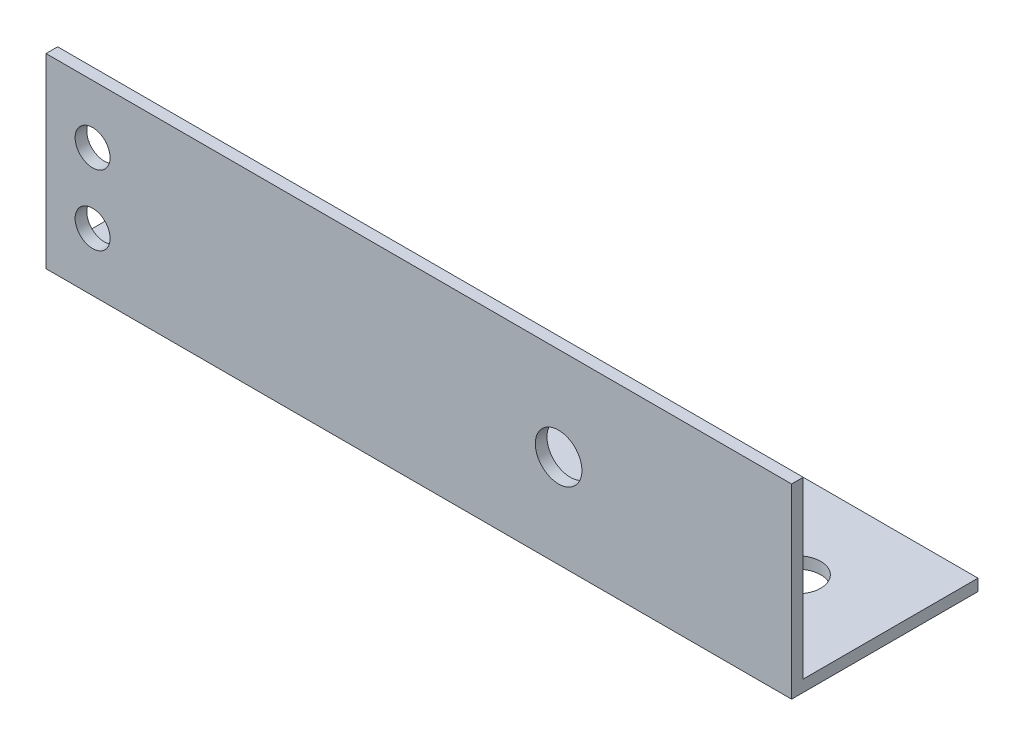
SolidWorks part; units mm, degrees
ref_plane "Front Plane" through (0, 0, 0) normal (0, 0, 1) x (1, 0, 0)
ref_plane "Top Plane" through (0, 0, 0) normal (0, 1, 0) x (1, 0, 0)
ref_plane "Right Plane" through (0, 0, 0) normal (1, 0, 0) x (0, 0, -1)
sketch "Sketch1" plane through (0, 0, 0) normal (1, 0, 0) x (0, 0, -1)
  line L0 (0, 0) -> (0, 25.4)
  line L1 (0, 25.4) -> (-1.5875, 25.4)
  line L2 (-1.5875, 25.4) -> (-1.5875, 1.5875)
  line L3 (-1.5875, 1.5875) -> (-25.4, 1.5875)
  line L4 (-25.4, 1.5875) -> (-25.4, 0)
  line L5 (-25.4, 0) -> (0, 0)
  dimension "D1" = 25.4
  dimension "D2" = 25.4
  dimension "D3" = 1.5875
  dimension "D4" = 1.5875
extrude "Boss-Extrude1" add sketch "Sketch1" along normal blind 101.6 contours L0 L1 L2 L3 L4 L5
sketch "Sketch2" plane through (0, 1.5875, 0) normal (0, 1, 0) x (1, 0, 0)
  line L0 (0, -13.4937) -> (101.6, -13.4937) construction
  line L1 (0, -1.5875) -> (0, -25.4) construction
  line L2 (101.6, -1.5875) -> (101.6, -25.4) construction
  circle A0 centre (12.7, -13.4937) radius 3.175
  circle A1 centre (88.9, -13.4937) radius 3.175
  dimension "D1" = 6.35
  dimension "D2" = 12.7
  dimension "D3" = 12.7
extrude "Cut-Extrude1" cut sketch "Sketch2" against normal blind 101.6
sketch "Sketch3" plane through (0, 0, 1.5875) normal (0, 0, 1) x (1, 0, 0)
  line L0 (0, 0) -> (0, 25.4) construction
  line L1 (0, 12.7) -> (101.6, 12.7) construction
  line L2 (101.6, 25.4) -> (101.6, 1.5875) construction
  line L3 (6.35, 7.9375) -> (6.35, 17.4625) construction
  circle A0 centre (69.85, 12.7) radius 3.175
  circle A1 centre (6.35, 17.4625) radius 2.3813
  circle A2 centre (6.35, 7.9375) radius 2.3813
  point P13 (6.35, 12.7)
  dimension "D2" = 4.7625
  dimension "D3" = 6.35
  dimension "D1" = 9.525
  dimension "D4" = 6.35
  dimension "D5" = 31.75
extrude "Cut-Extrude2" cut sketch "Sketch3" against normal blind 101.6
mirror "Mirror1" about plane through (101.6, 0, 0) normal (0, 0, 1) of "Boss-Extrude1", "Cut-Extrude1", "Cut-Extrude2"
sketch "Sketch4" plane through (0, 0, 0) normal (-1, 0, 0) x (0, 0, 1)
  line L0 (0, 0) -> (0, 25.4) construction
  line L1 (25.4, 0) -> (-25.4, 0) construction
  line L2 (-1.5875, 25.4) -> (1.5875, 25.4) construction
  line L4 (0, 0) -> (29.6768, 0)
  line L5 (0, 0) -> (0, 30.9422)
  line L6 (0, 30.9422) -> (29.6768, 30.9422)
  line L7 (29.6768, 0) -> (29.6768, 30.9422)
extrude "Cut-Extrude3" cut sketch "Sketch4" against normal blind 101.6
